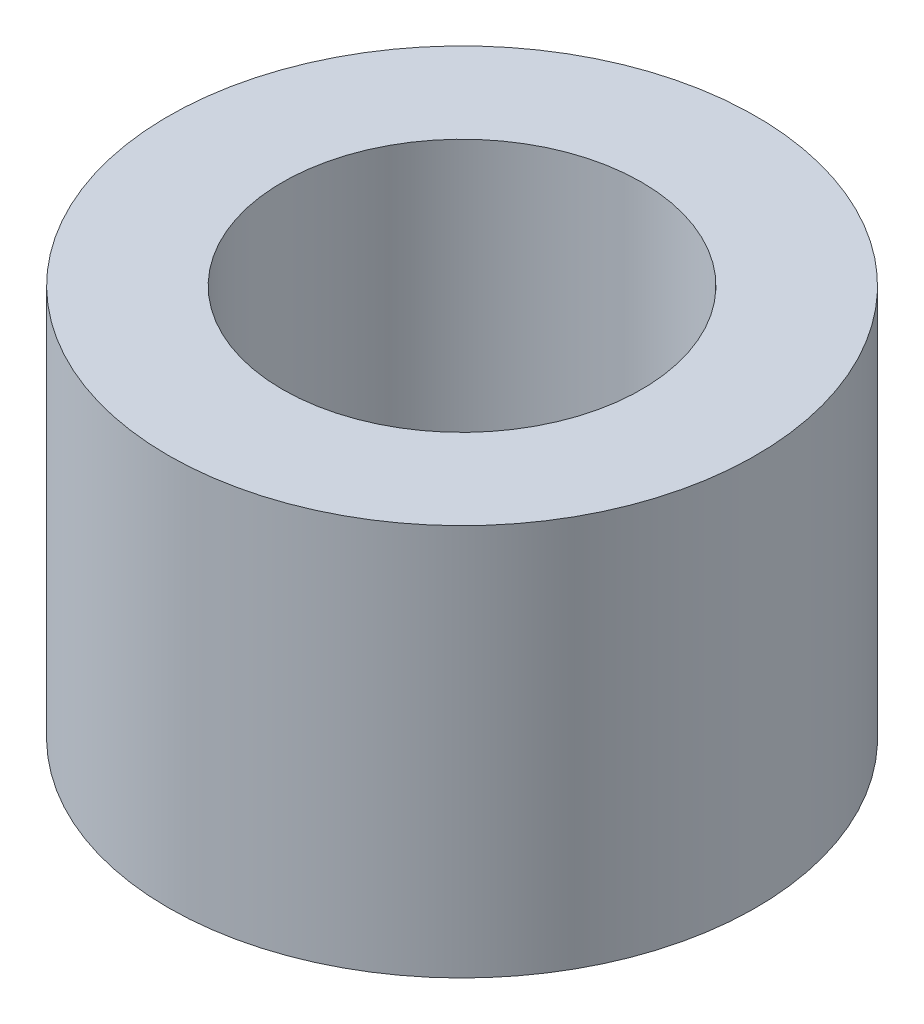
SolidWorks part; units mm, degrees
ref_plane "Front Plane" through (0, 0, 0) normal (0, 0, 1) x (1, 0, 0)
ref_plane "Top Plane" through (0, 0, 0) normal (0, 1, 0) x (1, 0, 0)
ref_plane "Right Plane" through (0, 0, 0) normal (1, 0, 0) x (0, 0, -1)
sketch "Sketch1" plane through (0, 0, 0) normal (0, 1, 0) x (1, 0, 0)
  circle A0 centre (0, 0) radius 2.25
  circle A1 centre (0, 0) radius 1.375
  dimension "D1" = 2.75
  dimension "D2" = 4.5
extrude "Boss-Extrude1" add sketch "Sketch1" along normal blind 3
equation "\"id\"= 2.75mm"
equation "\"D2@Sketch1\"=\"OD\""
equation "\"OD\" = 4.5mm"
equation "\"D1@Sketch1\"=\"id\""
